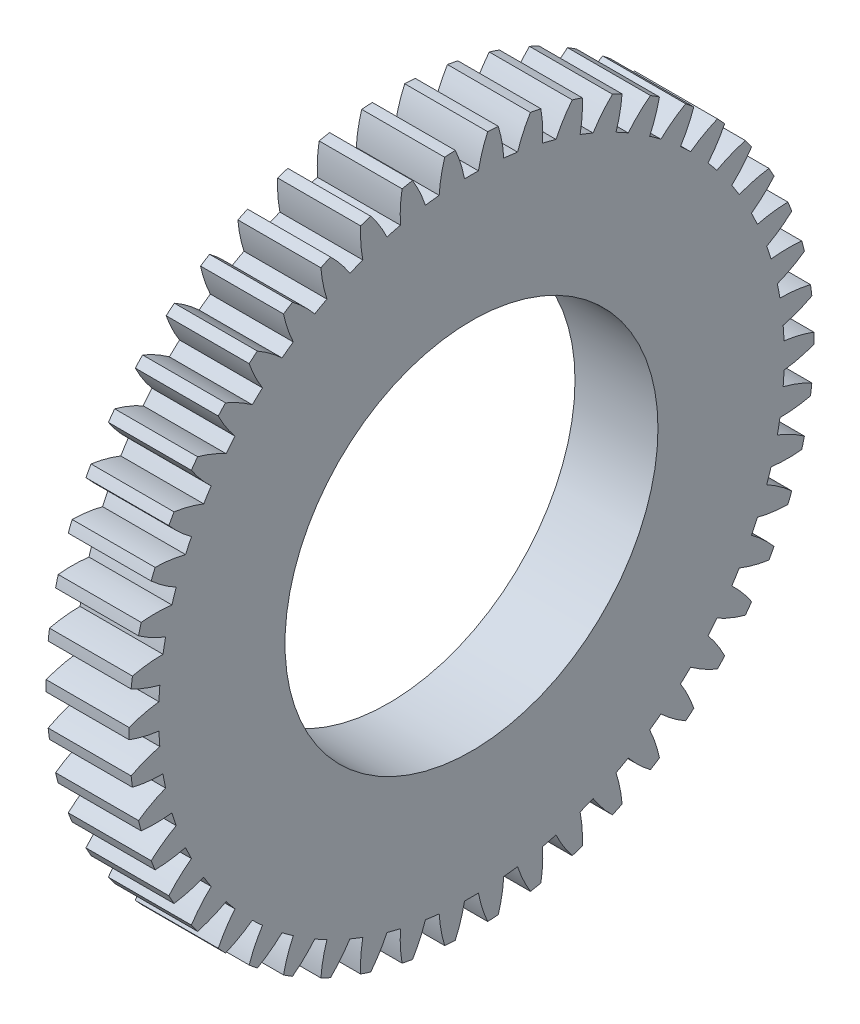
SolidWorks part; units mm, degrees
ref_plane "Plane1" through (0, 0, 0) normal (0, 0, 1) x (1, 0, 0)
ref_plane "Plane2" through (0, 0, 0) normal (0, 1, 0) x (1, 0, 0)
ref_plane "Plane3" through (0, 0, 0) normal (1, 0, 0) x (0, 0, -1)
sketch "HoldingSke" plane through (0, 0, 0) normal (0, 1, 0) x (1, 0, 0)
  line L0 (0, 0) -> (130.6144, -155.6602)
  line L1 (-15, 0) -> (100, 0) construction
  line L2 (0, 0) -> (-2.1039, 2.3779)
  line L3 (0, 0) -> (-11.863, 4.5341)
  line L4 (0, 0) -> (5.5511, 6.6156)
  line L5 (0, 0) -> (-47.5972, -17.7524)
  line L6 (0, 0) -> (-16.5793, -11.1861)
  line L7 (-2.1039, 2.3779) -> (8.8308, 51.9871)
  line L8 (-76.2, 54.61) -> (-75.184, 54.61)
  line L9 (-67.7845, 28.3722) -> (-49.3413, 33.142)
  line L10 (-76.2, 71.12) -> (104.1128, 71.12)
  line L11 (0, 0) -> (-20, 0)
  line L12 (-76.2, 101.6) -> (-76.0857, 101.6)
  line L13 (24.9733, 27.94) -> (52.9518, 28.4284)
  line L14 (24.9733, 27.94) -> (24.9746, 27.94)
  line L15 (24.9733, 27.94) -> (100.4006, 29.5858)
  circle A0 centre (0, 0) radius 0.3969
  circle A1 centre (0, 0) radius 38.1
  circle A2 centre (0, 0) radius 38.1
  circle A3 centre (0, 0) radius 0.3969
  dimension "MHD" = 76.2
  dimension "Hub_dia" = 76.2
  dimension "Bore" = 0.7937
  dimension "MBD" = 0.7937
  dimension "Num_teeth" = 50
  dimension "Pitch" = 203.2
  dimension "Overall_len" = 50.8
  dimension "Show_teeth" = 50
  dimension "Thickness" = 20
  dimension "OAL" = 50.8001
  dimension "T_dim" = 1.016
  dimension "Ap" = 14.5
  dimension "H" = 19.05
  dimension "Pitch_radius" = 180.3128
  dimension "Width" = 20
  dimension "Backlash" = 0.1143
  dimension "Addendum_fac" = 1
  dimension "Dedendum_fac" = 1.25
  dimension "Clearance_fac" = 0.25
  dimension "Dedendum_add" = 0.0013
sketch "BasProSke" plane through (0, 0, 0) normal (0, 1, 0) x (1, 0, 0)
  line L0 (-10, 0) -> (60, 0) construction
  line L1 (0, 0) -> (0, 82.55)
  line L2 (0, 0) -> (20, 0)
  line L3 (20, 0) -> (20, 82.55)
  line L4 (20, 82.55) -> (0, 82.55)
  dimension "Thickness" = 20
  dimension "Diameter" = 165.1
revolve "Base-Revolve" add sketch "BasProSke" angle 360 about L0
sketch "TooCutSke" plane through (0, 0, 0) normal (1, 0, 0) x (0, 0, -1)
  line L1 (0, 0) -> (0, 107) construction
  line L2 (0, 0) -> (-2.6932, 79.3293) construction
  line L3 (0, 0) -> (-9.9638, 158.3706) construction
  line L4 (-2.6932, 79.3293) -> (-4.9819, 79.1853) construction
  arc A0 (1.6786, 75.3863) -> (-1.6786, 75.3863) centre (0, 0) ccw
  arc A1 (3.9137, 82.4826) -> (-3.9137, 82.4826) centre (0, 0) ccw
  circle A2 centre (0, 0) radius 79.375 construction
  circle A3 centre (0, 0) radius 76.8467 construction
  arc A4 (-1.6786, 75.3863) -> (-3.9137, 82.4826) centre (-32.8709, 69.4617) ccw
  arc A5 (3.9137, 82.4826) -> (1.6786, 75.3863) centre (32.8709, 69.4617) ccw
  dimension "Root_dia" = 150.81
  dimension "Overcut_dia" = 165.1508
  dimension "Pitch_dia" = 158.75
  dimension "Base_dia" = 153.6934
  dimension "Flank_rad" = 31.75
  dimension "Half_ang" = 3.6
  dimension "Half_CT" = 2.2932
extrude "ToothCut" cut sketch "TooCutSke" along normal through all
fillet "Breaks" [suppressed] radius 0.0635
fillet "RootFillets" [suppressed] radius 0.795
pattern_circular "TeethCuts" count 50 every 7.2 about axis through (-10, 0, 0) along (1, 0, 0) of "ToothCut", "RootFillets", "Breaks"
sketch "HubNeaOneSke" plane through (0, 0, 0) normal (-1, 0, 0) x (0, 0, 1)
  circle A0 centre (0, 0) radius 38.1
  dimension "Diameter" = 76.2
extrude "HubNearOne" [suppressed] add sketch "HubNeaOneSke" along normal blind 30.8001
sketch "HubNeaBotSke" plane through (0, 0, 0) normal (-1, 0, 0) x (0, 0, 1)
  circle A0 centre (0, 0) radius 38.1
  dimension "Diameter" = 76.2
extrude "HubNearBoth" [suppressed] add sketch "HubNeaBotSke" along normal blind 15.4
ref_plane "FarPln" through (20, 0, 0) normal (1, 0, 0) x (0, 0, -1)
sketch "HubFarSke" plane through (20, 0, 0) normal (1, 0, 0) x (0, 0, -1)
  circle A0 centre (0, 0) radius 38.1
  dimension "Diameter" = 76.2
extrude "HubFar" [suppressed] add sketch "HubFarSke" along normal blind 15.4
sketch "BorSke" plane through (0, 0, 0) normal (1, 0, 0) x (0, 0, -1)
  circle A0 centre (0, 0) radius 0.3969
  dimension "Diameter" = 0.7937
extrude "Bore" cut sketch "BorSke" along normal mid plane 101.6001
sketch "KeySke" plane through (0, 0, 0) normal (1, 0, 0) x (0, 0, -1)
  line L0 (-0.127, 0) -> (-0.127, 0.6191)
  line L1 (-0.127, 0.6191) -> (0.127, 0.6191)
  line L2 (0.127, 0.6191) -> (0.127, 0)
  line L3 (0, 0) -> (0, 34) construction
  line L4 (-0.127, 0) -> (0.127, 0)
  dimension "Offset" = 0.6191
  dimension "Width" = 0.254
extrude "Keyway" [suppressed] cut sketch "KeySke" along normal mid plane 101.6001
pattern_circular "Keyway2" [suppressed] count 2 every 90 about axis through (-10, 0, 0) along (1, 0, 0)
sketch "Sketch1" plane through (20, 0, 0) normal (1, 0, 0) x (0, 0, -1)
  circle A0 centre (0, 0) radius 44.958
extrude "Cut-Extrude1" cut sketch "Sketch1" against normal blind 20.32
equation "' \"Pitch@HoldingSke\" = 4"
equation "' \"Num_teeth@HoldingSke\" = 12"
equation "' \"Ap@HoldingSke\" =  20"
equation "' \"Ap@HoldingSke\" = 20"
equation "' \"Width@HoldingSke\" = 0.5"
equation "' \"Hub_dia@HoldingSke\"= 1"
equation "' \"Hub_dia@HoldingSke\" = 1"
equation "' \"Overall_len@HoldingSke\" = 1.0"
equation "' \"Bore@HoldingSke\" = 0.75"
equation "' \"T_dim@HoldingSke\" = 0.85"
equation "' \"Width@KeySke\" = 0.25"
equation "' \"Show_teeth@HoldingSke\" = 13"
equation "' \"Backlash@HoldingSke\" = 0.009"
equation "' \"Addendum_fac@HoldingSke\" = 1.0"
equation "' \"Dedendum_fac@HoldingSke\" = 1.25"
equation "' \"Dedendum_add@HoldingSke\" = 0.00005"
equation "' \"Clearance_fac@HoldingSke\" = 0.25"
equation "' \"Pitch@HoldingSke\" = 0.5"
equation "' \"Num_teeth@HoldingSke\" = 23"
equation "' \"Show_teeth@HoldingSke\" = 23"
equation "' \"Backlash@HoldingSke\" = 0.0375"
equation "\"Overcut_dia@TooCutSke\" = (\"Num_teeth@HoldingSke\" + 2 * \"Addendum_fac@HoldingSke\") / \"Pitch@HoldingSke\" + 0.002"
equation "\"Pitch_dia@TooCutSke\" = \"Num_teeth@HoldingSke\" / \"Pitch@HoldingSke\""
equation "\"Base_dia@TooCutSke\" = \"Num_teeth@HoldingSke\" / \"Pitch@HoldingSke\" * cos((\"Ap@HoldingSke\"  * 3.14159265 / 180))"
equation "\"Root_dia@TooCutSke\" = (\"Num_teeth@HoldingSke\" + 2) / \"Pitch@HoldingSke\" - 2 * (\"Addendum_fac@HoldingSke\" + \"Dedendum_fac@HoldingSke\") / \"Pitch@HoldingSke\" - \"Dedendum_add@HoldingSke\" * 2"
equation "\"Half_ang@TooCutSke\" = 180 / \"Num_teeth@HoldingSke\""
equation "\"Half_CT@TooCutSke\" = \"Num_teeth@HoldingSke\" / \"Pitch@HoldingSke\" * sin((3.14159265 / 2 / \"Num_teeth@HoldingSke\")) / 2 - 7 * \"Backlash@HoldingSke\" / 4"
equation "\"Flank_rad@TooCutSke\" = \"Num_teeth@HoldingSke\" / \"Pitch@HoldingSke\" / 5"
equation "\"Radius@RootFillets\" = \"Clearance_fac@HoldingSke\" / \"Pitch@HoldingSke\" + \"Dedendum_add@HoldingSke\""
equation "\"Break_rad@Breaks\" = 0.02 / \"Pitch@HoldingSke\""
equation "\"Thickness@HoldingSke\" = \"Width@HoldingSke\""
equation "\"OAL@HoldingSke\" = \"Thickness@HoldingSke\""
equation "\"MHD@HoldingSke\" = (\"Num_teeth@HoldingSke\" + 2) / \"Pitch@HoldingSke\" - 2 * (\"Addendum_fac@HoldingSke\" + \"Dedendum_fac@HoldingSke\")  / \"Pitch@HoldingSke\" - \"Dedendum_add@HoldingSke\" * 2"
equation "\"MBD@HoldingSke\" = (\"Num_teeth@HoldingSke\" + 2) / \"Pitch@HoldingSke\" - 2 * (\"Addendum_fac@HoldingSke\" + \"Dedendum_fac@HoldingSke\")  / \"Pitch@HoldingSke\" - \"Dedendum_add@HoldingSke\" * 2 - 0.002"
equation "\"MHD@HoldingSke\" = ((sgn( \"MHD@HoldingSke\" - \"Hub_dia@HoldingSke\" )-1)*( \"MHD@HoldingSke\" - \"Hub_dia@HoldingSke\" ))/-2+ \"Hub_dia@HoldingSke\""
equation "\"MBD@HoldingSke\" = ((sgn( \"MBD@HoldingSke\" - \"Bore@HoldingSke\" )-1)*( \"MBD@HoldingSke\" - \"Bore@HoldingSke\" ))/-2+ \"Bore@HoldingSke\""
equation "\"OAL@HoldingSke\" = ((sgn( \"OAL@HoldingSke\" - \"Overall_len@HoldingSke\" )+1)*( \"OAL@HoldingSke\" - \"Overall_len@HoldingSke\" ))/2 + \"Overall_len@HoldingSke\" + 0.000002"
equation "\"Num_teeth@TeethCuts\" = int( \"Show_teeth@HoldingSke\" ) + 1"
equation "\"Num_teeth@TeethCuts\" = ((sgn( \"Num_teeth@TeethCuts\" - \"Num_teeth@HoldingSke\" )-1)*( \"Num_teeth@TeethCuts\" - \"Num_teeth@HoldingSke\" ))/-2+ \"Num_teeth@HoldingSke\""
equation "\"Num_teeth@TeethCuts\" = ((sgn( \"Num_teeth@TeethCuts\" - 2.0)+1)*( \"Num_teeth@TeethCuts\" - 2.0))/2 +2.0"
equation "\"Angle@TeethCuts\" = 360.0 / \"Num_teeth@HoldingSke\""
equation "\"Diameter@BasProSke\" = (\"Num_teeth@HoldingSke\" + 2 * \"Addendum_fac@HoldingSke\") / \"Pitch@HoldingSke\""
equation "\"Thickness@BasProSke\"  = \"Thickness@HoldingSke\""
equation "' \"Fillet_rad@BasProSke\" =  \"Thickness@HoldingSke\" * 0.05"
equation "' \"Fillet_rad@BasProSke\" = \"Thickness@HoldingSke\" * 0.05"
equation "\"MHD@HoldingSke\" = ((sgn( \"MHD@HoldingSke\" - \"Root_dia@TooCutSke\" )-1)*( \"MHD@HoldingSke\" - \"Root_dia@TooCutSke\" ))/-2+ \"Root_dia@TooCutSke\""
equation "\"Diameter@HubNeaOneSke\" = \"MHD@HoldingSke\""
equation "\"Length@HubNearOne\" = \"OAL@HoldingSke\" - \"Thickness@BasProSke\""
equation "\"Diameter@HubNeaBotSke\" = \"MHD@HoldingSke\""
equation "\"Length@HubNearBoth\" = ( \"OAL@HoldingSke\" - \"Thickness@BasProSke\" ) / 2.0"
equation "\"Thickness@FarPln\" = \"Thickness@BasProSke\""
equation "\"Diameter@HubFarSke\" = \"MHD@HoldingSke\""
equation "\"Length@HubFar\" = ( \"OAL@HoldingSke\" - \"Thickness@BasProSke\" ) / 2.0"
equation "\"Diameter@BorSke\" = \"MBD@HoldingSke\""
equation "\"D1@Bore\" = \"OAL@HoldingSke\" * 2.0"
equation "\"D1@Keyway\" = \"OAL@HoldingSke\" * 2.0"
equation "\"Offset@KeySke\" = \"T_dim@HoldingSke\" - \"MBD@HoldingSke\" / 2.0"
